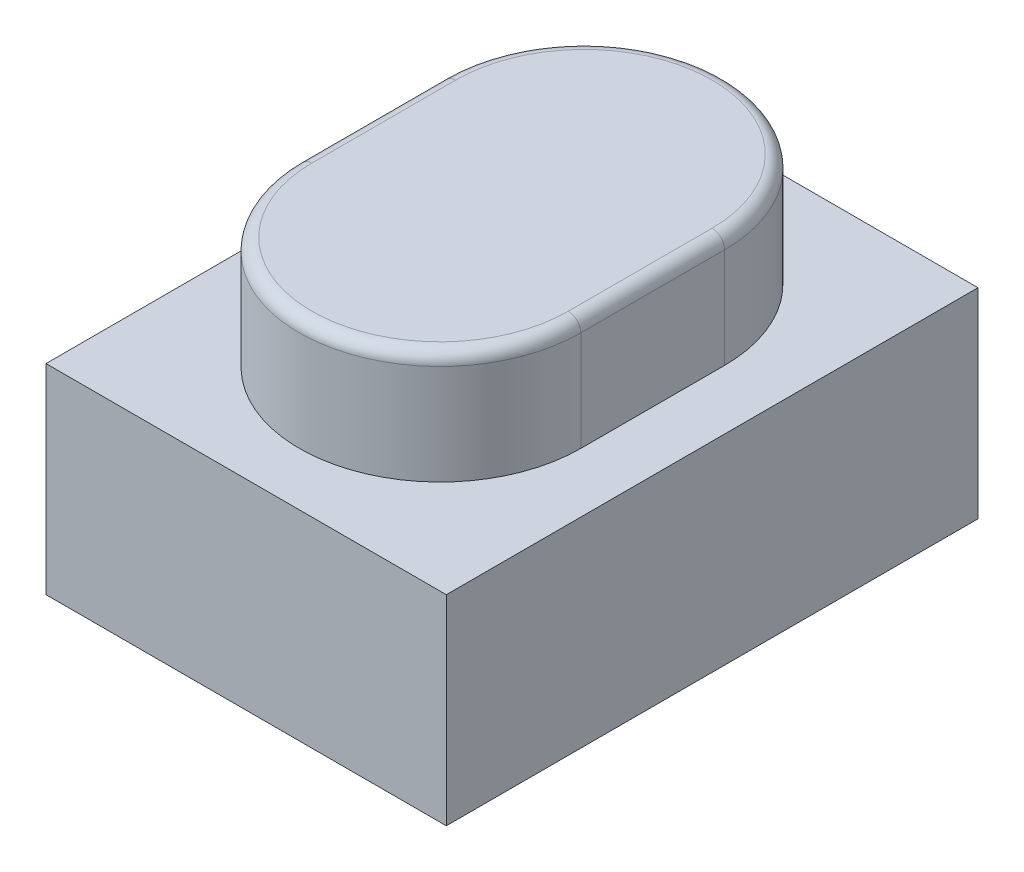
SolidWorks part; units mm, degrees
ref_plane "Front Plane" through (0, 0, 0) normal (0, 0, 1) x (1, 0, 0)
ref_plane "Top Plane" through (0, 0, 0) normal (0, 1, 0) x (1, 0, 0)
ref_plane "Right Plane" through (0, 0, 0) normal (1, 0, 0) x (0, 0, -1)
sketch "BaseS" plane through (0, 0, 0) normal (0, 1, 0) x (1, 0, 0)
  line L1 (-1.6, 2.125) -> (1.6, 2.125)
  line L2 (-1.6, 2.125) -> (-1.6, -2.125)
  line L3 (-1.6, -2.125) -> (1.6, -2.125)
  line L4 (1.6, 2.125) -> (1.6, -2.125)
  line L5 (-1.6, 2.125) -> (1.6, -2.125) construction
  line L6 (-1.6, -2.125) -> (1.6, 2.125) construction
  point P0 (0, 0)
  dimension "Width" = 3.2
  dimension "Length" = 4.25
extrude "Base" add sketch "BaseS" along normal blind 1.6
sketch "ButtonS" plane through (0, 1.6, 0) normal (0, 1, 0) x (1, 0, 0)
  line L0 (0, 0.575) -> (0, -0.575) construction
  line L1 (1.125, 0.575) -> (1.125, -0.575)
  line L2 (-1.125, 0.575) -> (-1.125, -0.575)
  arc A0 (1.125, 0.575) -> (-1.125, 0.575) centre (0, 0.575) ccw
  arc A1 (-1.125, -0.575) -> (1.125, -0.575) centre (0, -0.575) ccw
  point P2 (0, 0)
  point P8 (0, 0.6335)
  dimension "Width" = 2.25
  dimension "Height" = 1.15
extrude "Button" add sketch "ButtonS" along normal blind 0.9
fillet "BF" radius 0.1 4 edges at (1.125, 2.5, 0) (0, 2.5, 1.7) (-1.125, 2.5, 0) (0, 2.5, -1.7)
